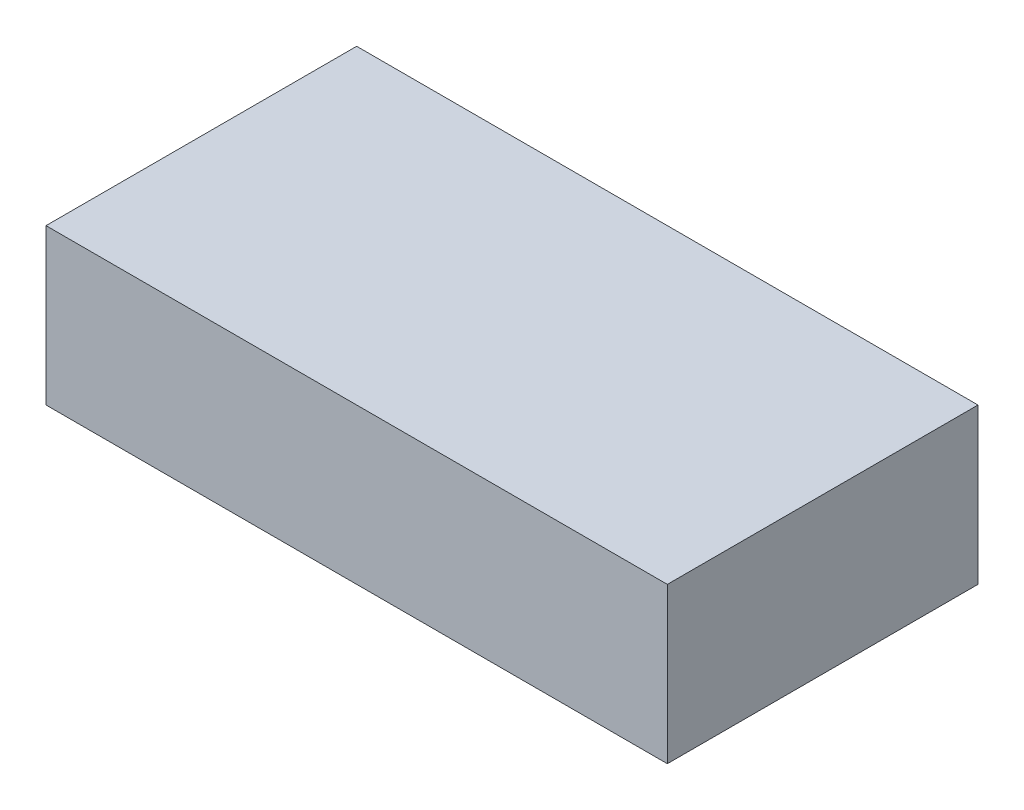
SolidWorks part; units mm, degrees
ref_plane "Plan de face" through (0, 0, 0) normal (0, 0, 1) x (1, 0, 0)
ref_plane "Plan de dessus" through (0, 0, 0) normal (0, 1, 0) x (1, 0, 0)
ref_plane "Plan de droite" through (0, 0, 0) normal (1, 0, 0) x (0, 0, -1)
sketch "Esquisse1" plane through (0, 0, 0) normal (0, 1, 0) x (1, 0, 0)
  line L1 (0, 0) -> (2, 0)
  line L2 (0, 0) -> (0, 1)
  line L3 (0, 1) -> (2, 1)
  line L4 (2, 0) -> (2, 1)
  dimension "D1" = 2
  dimension "D2" = 1
extrude "Extrusion1" add sketch "Esquisse1" along normal blind 0.5
